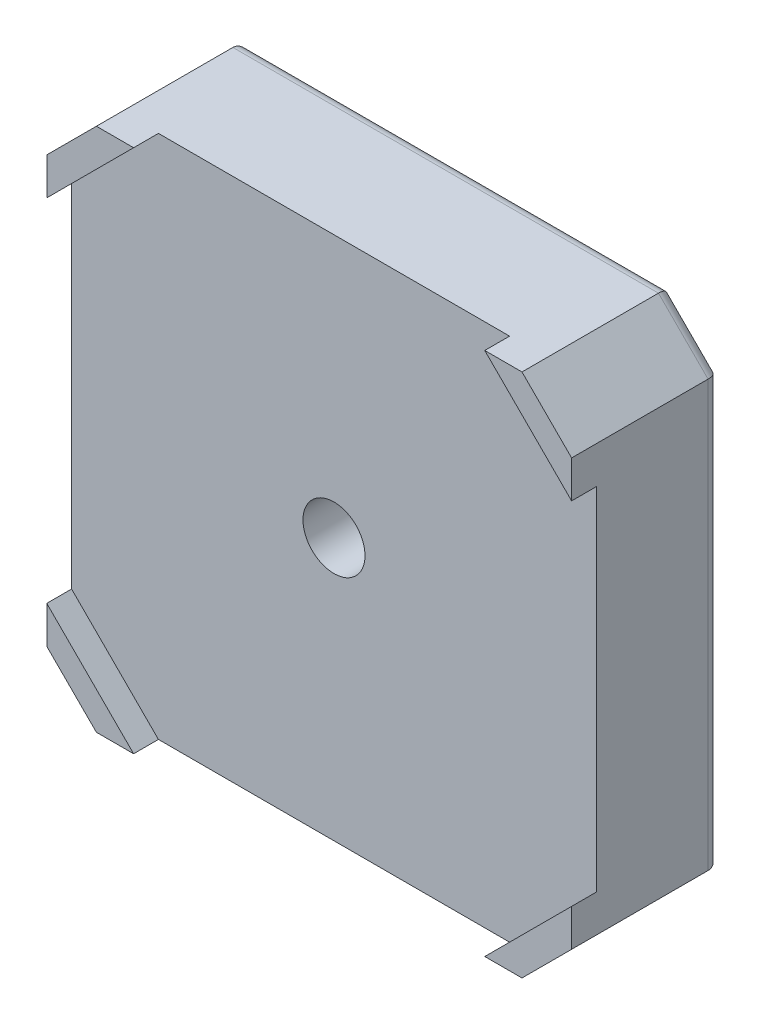
SolidWorks part; units mm, degrees
material "Acciaio inossidabile al cromo"
ref_plane "Piano frontale" through (0, 0, 0) normal (0, 0, 1) x (1, 0, 0)
ref_plane "Piano superiore" through (0, 0, 0) normal (0, 1, 0) x (1, 0, 0)
ref_plane "Piano destro" through (0, 0, 0) normal (1, 0, 0) x (0, 0, -1)
sketch "Schizzo1" plane through (0, 0, 0) normal (0, 0, 1) x (1, 0, 0)
  line L0 (-21.15, 17.15) -> (-17.15, 21.15)
  line L1 (-17.15, -21.15) -> (17.15, -21.15)
  line L2 (-21.15, -17.15) -> (-21.15, 17.15)
  line L3 (-17.15, 21.15) -> (17.15, 21.15)
  line L4 (21.15, -17.15) -> (21.15, 17.15)
  line L5 (-21.15, -21.15) -> (21.15, 21.15) construction
  line L6 (-21.15, 21.15) -> (21.15, -21.15) construction
  line L7 (17.15, 21.15) -> (21.15, 17.15)
  line L8 (17.15, -21.15) -> (21.15, -17.15)
  line L9 (-21.15, -17.15) -> (-17.15, -21.15)
  point P0 (0, 0)
  dimension "D1" = 42.3
  dimension "D2" = 42.3
extrude "Estrusione-Estrusione1" add sketch "Schizzo1" along normal blind 12
sketch "Schizzo2" plane through (0, 0, 12) normal (0, 0, 1) x (1, 0, 0)
  line L0 (-21.15, 14.15) -> (-14.15, 21.15)
  line L1 (-14.15, -21.15) -> (14.15, -21.15)
  line L2 (-21.15, -14.15) -> (-21.15, 14.15)
  line L3 (-14.15, 21.15) -> (14.15, 21.15)
  line L4 (21.15, -14.15) -> (21.15, 14.15)
  line L5 (-21.15, -21.15) -> (21.15, 21.15) construction
  line L6 (-21.15, 21.15) -> (21.15, -21.15) construction
  line L7 (14.15, 21.15) -> (21.15, 14.15)
  line L8 (14.15, -21.15) -> (21.15, -14.15)
  line L9 (-21.15, -14.15) -> (-14.15, -21.15)
  point P0 (0, 0)
  dimension "D1" = 42.3
  dimension "D2" = 42.3
extrude "Taglio-Estrusione1" cut sketch "Schizzo2" against normal blind 2
sketch "Schizzo3" plane through (0, 0, 0) normal (0, 0, -1) x (-1, 0, 0)
  circle A0 centre (0, 0) radius 11
  dimension "D1" = 22
extrude "Estrusione-Estrusione2" add sketch "Schizzo3" along normal blind 2
sketch "Schizzo4" plane through (0, 0, -2) normal (0, 0, -1) x (-1, 0, 0)
  circle A0 centre (0, 0) radius 5.5
  dimension "D1" = 11
extrude "Taglio-Estrusione2" cut sketch "Schizzo4" against normal blind 7
sketch "Schizzo5" plane through (0, 0, 5) normal (0, 0, -1) x (-1, 0, 0)
  circle A0 centre (0, 0) radius 2.5
  dimension "D1" = 5
extrude "Taglio-Estrusione3" cut sketch "Schizzo5" against normal through all
fillet "Raccordo1" radius 1 8 edges at (-19.15, 19.15, 0) (-21.15, 0, 0) (-19.15, -19.15, 0) (0, -21.15, 0) (19.15, -19.15, 0) (21.15, 0, 0) (19.15, 19.15, 0) (0, 21.15, 0)
fillet "Raccordo2" radius 0.5 3 edges at (-5.5, 0, -2) (-5.5, 0, 5) (-11, 0, -2)
sketch "Schizzo6" plane through (0, 0, 0) normal (0, 0, -1) x (-1, 0, 0)
  line L1 (-15.5, -15.5) -> (15.5, -15.5) construction
  line L2 (-15.5, -15.5) -> (-15.5, 15.5) construction
  line L3 (-15.5, 15.5) -> (15.5, 15.5) construction
  line L4 (15.5, -15.5) -> (15.5, 15.5) construction
  line L5 (-15.5, -15.5) -> (15.5, 15.5) construction
  line L6 (-15.5, 15.5) -> (15.5, -15.5) construction
  circle A0 centre (-15.5, 15.5) radius 1.5
  circle A1 centre (15.5, 15.5) radius 1.5
  circle A2 centre (15.5, -15.5) radius 1.5
  circle A3 centre (-15.5, -15.5) radius 1.5
  point P0 (0, 0)
  dimension "D2" = 3
  dimension "D1" = 31
extrude "Taglio-Estrusione4" cut sketch "Schizzo6" against normal blind 3
fillet "Raccordo3" radius 0.5 4 edges at (14, -15.5, 0) (-17, -15.5, 0) (-17, 15.5, 0) (14, 15.5, 0)
